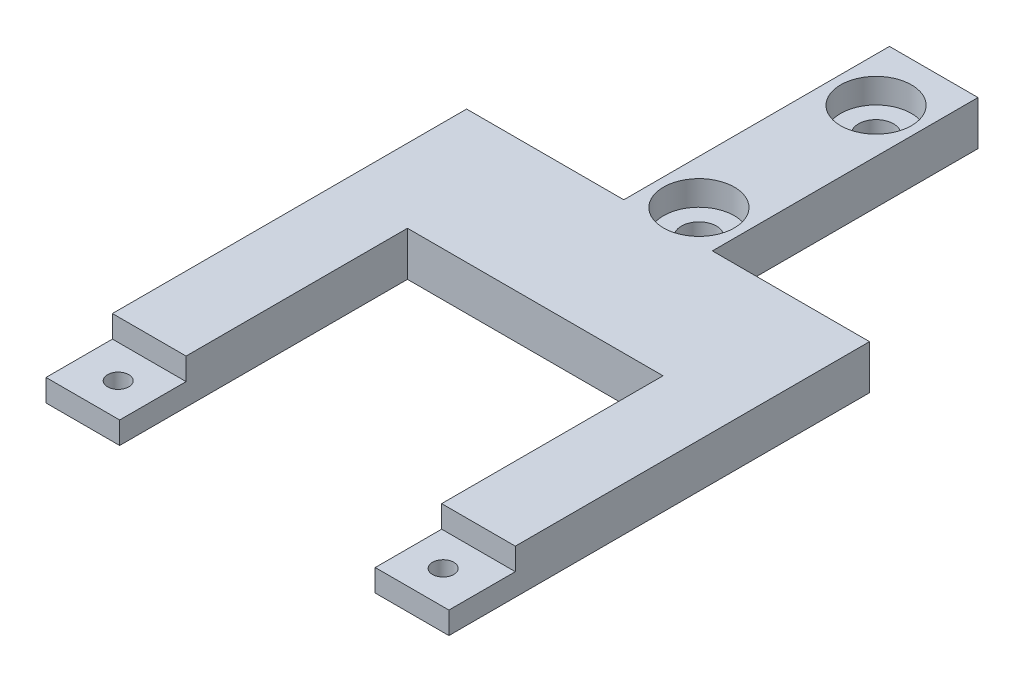
SolidWorks part; units mm, degrees
ref_plane "Front Plane" through (0, 0, 0) normal (0, 0, 1) x (1, 0, 0)
ref_plane "Top Plane" through (0, 0, 0) normal (0, 1, 0) x (1, 0, 0)
ref_plane "Right Plane" through (0, 0, 0) normal (1, 0, 0) x (0, 0, -1)
sketch "Sketch1" plane through (0, 0, 0) normal (0, 1, 0) x (1, 0, 0)
  line L1 (-14.4463, 15.0812) -> (14.4462, 15.0812)
  line L2 (-14.4463, 15.0812) -> (-14.4463, -15.0812)
  line L3 (-14.4463, -15.0812) -> (14.4462, -15.0812)
  line L4 (14.4462, 15.0812) -> (14.4462, -15.0812)
  line L5 (-9.1631, -15.0812) -> (9.1631, -15.0812)
  line L6 (-9.1631, -15.0812) -> (-9.1631, 5.5562)
  line L7 (-9.1631, 5.5562) -> (9.1631, 5.5562)
  line L8 (9.1631, -15.0812) -> (9.1631, 5.5562)
  line L9 (-3.175, 15.0813) -> (3.175, 15.0813)
  line L10 (-3.175, 15.0813) -> (-3.175, 34.1313)
  line L11 (-3.175, 34.1313) -> (3.175, 34.1313)
  line L12 (3.175, 15.0813) -> (3.175, 34.1313)
  point P4 (0, 15.0813)
  point P6 (-14.4463, 0)
  point P11 (0, 5.5563)
  point P16 (0, 15.0813)
  dimension "D1" = 28.8925
  dimension "D2" = 30.1625
  dimension "D3" = 5.2832
  dimension "D4" = 9.525
  dimension "D5" = 6.35
  dimension "D6" = 19.05
extrude "Boss-Extrude1" add sketch "Sketch1" along normal mid plane 3.175 contours L8 L3 L4 L1 L2 L6 L7 | L10 L9 L12 L11
sketch "Sketch2" plane through (0, 1.5875, 0) normal (0, 1, 0) x (1, 0, 0)
  line L0 (-9.1631, -15.0812) -> (-9.1631, 5.5562) construction
  line L1 (-14.4463, -15.0812) -> (-9.1631, -15.0812)
  line L2 (-14.4463, -15.0812) -> (-14.4463, -10.3187)
  line L3 (-14.4463, -10.3187) -> (-9.1631, -10.3187)
  line L4 (-9.1631, -15.0812) -> (-9.1631, -10.3187)
  line L5 (14.4462, 15.0812) -> (14.4462, -15.0812) construction
  line L6 (9.1631, -15.0812) -> (14.4462, -15.0812)
  line L7 (9.1631, -15.0812) -> (9.1631, -10.3187)
  line L8 (9.1631, -10.3187) -> (14.4462, -10.3187)
  line L9 (14.4462, -15.0812) -> (14.4462, -10.3187)
  dimension "D1" = 4.7625
extrude "Cut-Extrude1" cut sketch "Sketch2" against normal blind 1.5875
sketch "Sketch3" plane through (0, 1.5875, 0) normal (0, 1, 0) x (1, 0, 0)
  line L2 (0, -1000) -> (0, 49000) construction
  line L3 (-14.4463, -10.3187) -> (-14.4463, -15.0812) construction
  line L5 (-3.175, 34.1313) -> (3.175, 34.1313) construction
  circle A0 centre (-11.6523, -12.7) radius 0.762
  circle A2 centre (11.6523, -12.7) radius 0.762
  circle A4 centre (0, 17.294) radius 1.2573
  circle A5 centre (0, 29.994) radius 1.2573
  dimension "D1" = 2.5146
  dimension "D2" = 1.524
  dimension "D3" = 2.794
  dimension "D5" = 12.7
  dimension "D6" = 4.1372
extrude "Cut-Extrude2" cut sketch "Sketch3" against normal up to surface (3.175 mm away) from surface at 0 up to face at (0, -1.5875, -6.6146) starting at face at (0, 1.5875, -8.2021)
thread "Thread8" [suppressed] pitch 0.3175 start angle 0, offset 0, length 0, pitch 0.3175, diameter 1.524
ref_plane "Plane9" through (-13.462, 0, 12.7) normal (0, 0, 1) x (-1, 0, 0)
sketch "Thread Profile9" plane through (-13.462, 0, 12.7) normal (0, 0, 1) x (-1, 0, 0)
  line L0 (0, 0) -> (0, 0.3175) construction
  line L11 (0, 0) -> (0, 0.2778)
  line L12 (0, 0.2778) -> (-0.1719, 0.1786)
  line L13 (-0.1719, 0.1786) -> (-0.1719, 0.0992)
  line L15 (-0.1719, 0.0992) -> (0, 0)
  line L17 (-0.1719, 0.1389) -> (0, 0.1389) construction
  point P2 (0, 0)
  dimension "Pitch" = 0.3175
  dimension "Profile_Angle" = 60
  dimension "Profile_Land" = 0.0794
  dimension "Profile_Height" = 0.1719
thread "Thread9" [suppressed] pitch 0.3175 start angle 0, offset 0, length 0, pitch 0.3175, diameter 1.524
ref_plane "Plane10" through (11.938, 0, 12.7) normal (0, 0, 1) x (-1, 0, 0)
sketch "Thread Profile10" plane through (11.938, 0, 12.7) normal (0, 0, 1) x (-1, 0, 0)
  line L0 (0, 0) -> (0, 0.3175) construction
  line L11 (0, 0) -> (0, 0.2778)
  line L12 (0, 0.2778) -> (-0.1719, 0.1786)
  line L13 (-0.1719, 0.1786) -> (-0.1719, 0.0992)
  line L15 (-0.1719, 0.0992) -> (0, 0)
  line L17 (-0.1719, 0.1389) -> (0, 0.1389) construction
  point P2 (0, 0)
  dimension "Pitch" = 0.3175
  dimension "Profile_Angle" = 60
  dimension "Profile_Land" = 0.0794
  dimension "Profile_Height" = 0.1719
sketch "Sketch25" plane through (-14.4463, 0, 0) normal (-1, 0, 0) x (0, 0, 1)
  line L1 (-34.1313, -1.5875) -> (17.4266, -1.5875)
  line L2 (-34.1313, -1.5875) -> (-34.1313, -4.2188)
  line L3 (-34.1313, -4.2188) -> (17.4266, -4.2188)
  line L4 (17.4266, -1.5875) -> (17.4266, -4.2188)
extrude "Cut-Extrude4" [suppressed] cut sketch "Sketch25" against normal through all
thread "Thread10" [suppressed] pitch 0.5292 start angle 0, offset 0, length 0, pitch 0.5292, diameter 2.5146
ref_plane "Plane11" through (-1.2573, 1.5875, -29.994) normal (0, 0, 1) x (-1, 0, 0)
sketch "Thread Profile11" plane through (-1.2573, 1.5875, -29.994) normal (0, 0, 1) x (-1, 0, 0)
  line L0 (0, 0) -> (0, 0.5292) construction
  line L11 (0, 0) -> (0, 0.463)
  line L12 (0, 0.463) -> (-0.2864, 0.2977)
  line L13 (-0.2864, 0.2977) -> (-0.2864, 0.1654)
  line L15 (-0.2864, 0.1654) -> (0, 0)
  line L17 (-0.2864, 0.2315) -> (0, 0.2315) construction
  point P2 (0, 0)
  dimension "Pitch" = 0.5292
  dimension "Profile_Angle" = 60
  dimension "Profile_Land" = 0.1323
  dimension "Profile_Height" = 0.2864
thread "Thread11" [suppressed] pitch 0.5292 start angle 0, offset 0, length 0, pitch 0.5292, diameter 2.5146
ref_plane "Plane12" through (-1.2573, 1.5875, -17.294) normal (0, 0, 1) x (-1, 0, 0)
sketch "Thread Profile12" plane through (-1.2573, 1.5875, -17.294) normal (0, 0, 1) x (-1, 0, 0)
  line L0 (0, 0) -> (0, 0.5292) construction
  line L11 (0, 0) -> (0, 0.463)
  line L12 (0, 0.463) -> (-0.2864, 0.2977)
  line L13 (-0.2864, 0.2977) -> (-0.2864, 0.1654)
  line L15 (-0.2864, 0.1654) -> (0, 0)
  line L17 (-0.2864, 0.2315) -> (0, 0.2315) construction
  point P2 (0, 0)
  dimension "Pitch" = 0.5292
  dimension "Profile_Angle" = 60
  dimension "Profile_Land" = 0.1323
  dimension "Profile_Height" = 0.2864
sketch "Sketch31" plane through (0, 1.5875, 0) normal (0, 1, 0) x (1, 0, 0)
  circle A0 centre (0, 17.294) radius 2.54
  circle A1 centre (0, 29.994) radius 2.54
  dimension "D1" = 5.08
  dimension "D2" = 5.08
extrude "Cut-Extrude5" cut sketch "Sketch31" against normal blind 1.778
